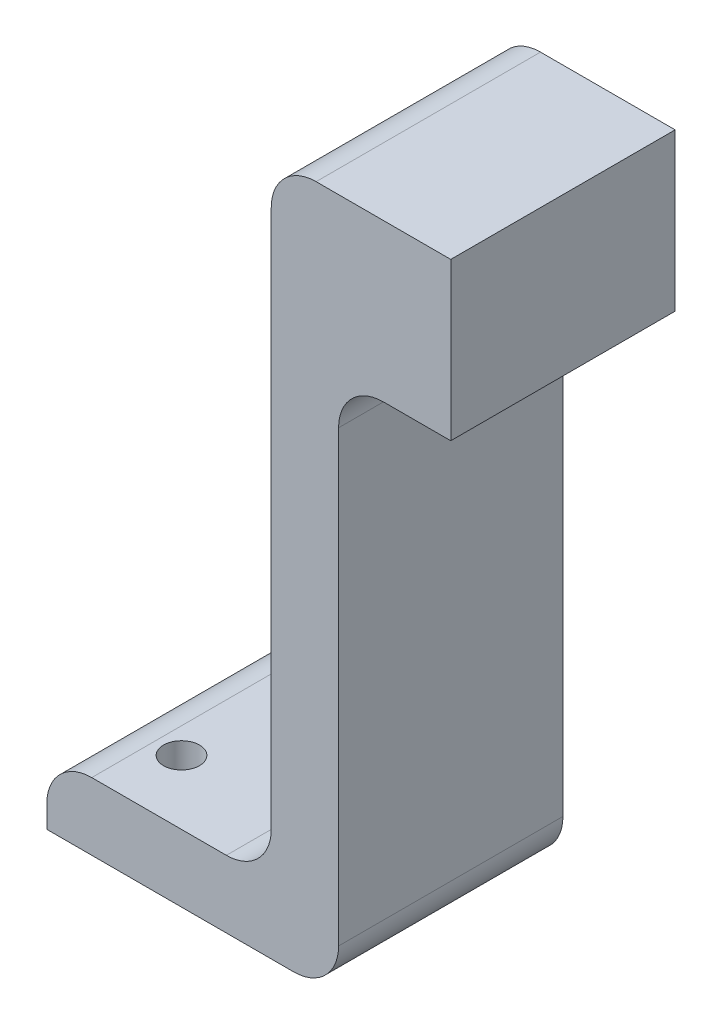
SolidWorks part; units mm, degrees
ref_plane "Front Plane" through (0, 0, 0) normal (0, 0, 1) x (1, 0, 0)
ref_plane "Top Plane" through (0, 0, 0) normal (0, 1, 0) x (1, 0, 0)
ref_plane "Right Plane" through (0, 0, 0) normal (1, 0, 0) x (0, 0, -1)
sketch "Sketch1" plane through (0, 0, 0) normal (0, 0, 1) x (1, 0, 0)
  line L0 (-0.4642, 0.25) -> (-0.4642, -5.75)
  line L5 (-0.4642, 0.25) -> (1.5358, 0.25)
  line L6 (-0.4642, 0.25) -> (-0.4642, 2)
  line L7 (-0.4642, 2) -> (1.5358, 2)
  line L8 (1.5358, 0.25) -> (1.5358, 2)
  line L9 (-0.4642, -5.75) -> (-2.9642, -5.75)
  line L10 (-0.4642, -5.75) -> (-0.4642, -5)
  line L11 (-0.4642, -5) -> (-2.9642, -5)
  line L12 (-2.9642, -5.75) -> (-2.9642, -5)
  line L13 (-0.4642, 0.25) -> (0.2858, 0.25)
  line L14 (-0.4642, -5.75) -> (0.2858, -5.75)
  line L15 (0.2858, 0.25) -> (0.2858, -5.75)
  dimension "D1" = 1.75
  dimension "D2" = 2
  dimension "D3" = 0
  dimension "D4" = 0.75
  dimension "D5" = 0.75
  dimension "D6" = 6
  dimension "D7" = 2.5
extrude "Boss-Extrude1" add sketch "Sketch1" along normal blind 1.875 and the other way blind 0.625 contours L5 L8 L7 L6 | L12 L9 L0 L11
fillet "Fillet1" radius 0.5 5 edges at (0.2858, 0.25, 0.625) (-0.4642, 2, 0.625) (-2.9642, -5, 0.625) (0.2858, -5.75, 0.625) (-0.4642, -5, 0.625)
hole_wizard "Ø0.4 (0.4) Diameter Hole1" positions "Sketch2" profile "Sketch3" hole size "Ø0.4" standard "DIN" end condition through all
sketch "Sketch2" plane through (0, -5, 0) normal (0, 1, 0) x (1, 0, 0)
  line L0 (-0.4642, 0) -> (-2.9642, 0) construction
  point P0 (-1.7142, 0)
  point P4 (-2.1785, -1.1606)
  dimension "D1" = 1.25
sketch "Sketch3" plane through (-1.7142, -5, 0) normal (1, 0, 0) x (0, 0, 1)
  line L0 (0, 0) -> (0, 0.75)
  line L1 (0, 0.75) -> (0.2, 0.75)
  line L2 (0.2, 0.75) -> (0.2, 0)
  line L5 (0.2, 0) -> (0, 0)
  line L11 (0, -6.35) -> (0, 107.95) construction
  dimension "Thru Hole Dia." = 0.4
  dimension "Thru Hole Depth" = 0.75
